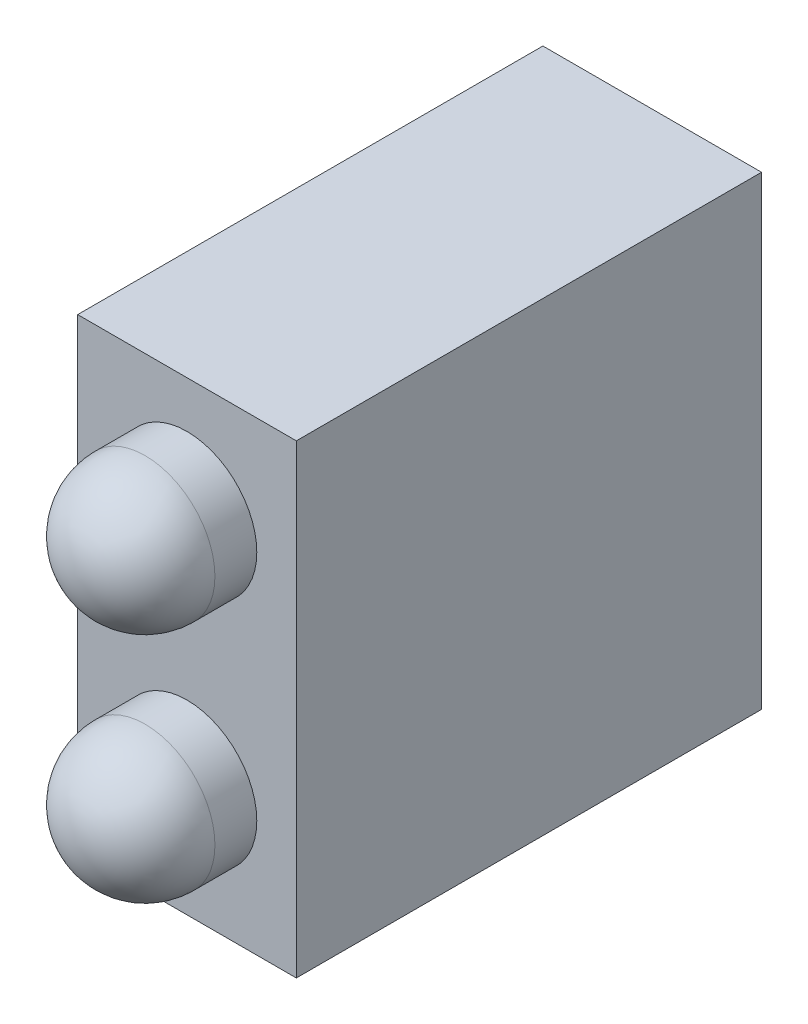
SolidWorks part; units mm, degrees
ref_plane "Alzado" through (0, 0, 0) normal (0, 0, 1) x (1, 0, 0)
ref_plane "Planta" through (0, 0, 0) normal (0, 1, 0) x (1, 0, 0)
ref_plane "Vista lateral" through (0, 0, 0) normal (1, 0, 0) x (0, 0, -1)
sketch "Croquis1" plane through (0, 0, 0) normal (0, 0, 1) x (1, 0, 0)
  line L1 (0, 0) -> (4.7, 0)
  line L2 (0, 0) -> (0, 10)
  line L3 (0, 10) -> (4.7, 10)
  line L4 (4.7, 0) -> (4.7, 10)
  dimension "D1" = 4.7
  dimension "D2" = 10
extrude "Extruir1" add sketch "Croquis1" along normal blind 10
sketch "Croquis2" plane through (0, 0, 10) normal (0, 0, 1) x (1, 0, 0)
  line L0 (4.7, 10) -> (0, 10) construction
  circle A0 centre (2.35, 7.5) radius 1.5
  circle A1 centre (2.35, 2.5) radius 1.5
  dimension "D1" = 3
  dimension "D2" = 3
  dimension "D3" = 2.5
  dimension "D4" = 5
extrude "Extruir2" add sketch "Croquis2" along normal blind 2.4 separate body
fillet "Redondeo1" radius 1.5 1 edges at (3.85, 7.5, 12.4)
fillet "Redondeo2" radius 1.5 1 edges at (3.85, 2.5, 12.4)
